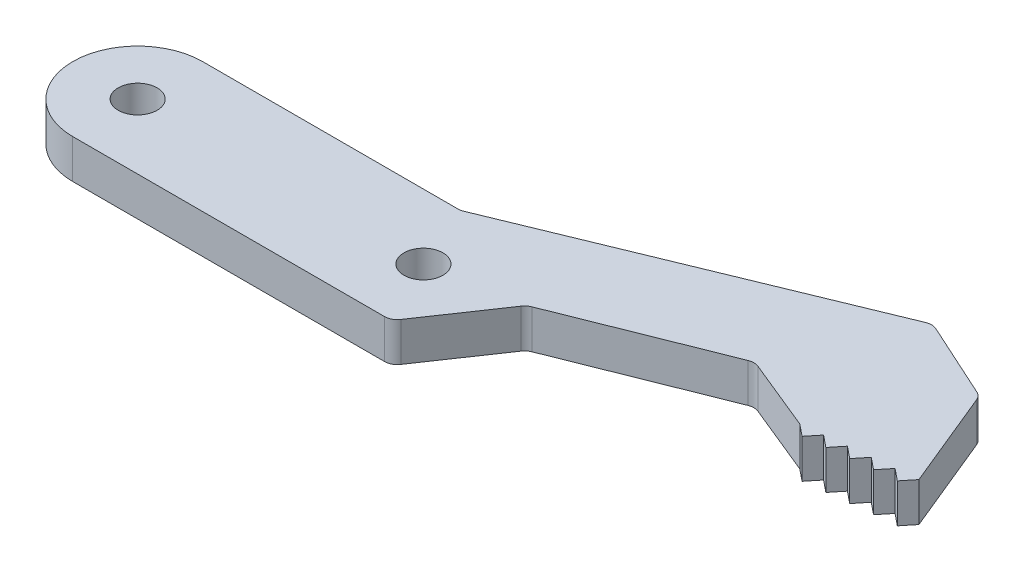
SolidWorks part; units mm, degrees
ref_plane "Front Plane" through (0, 0, 0) normal (0, 0, 1) x (1, 0, 0)
ref_plane "Top Plane" through (0, 0, 0) normal (0, 1, 0) x (1, 0, 0)
ref_plane "Right Plane" through (0, 0, 0) normal (1, 0, 0) x (0, 0, -1)
sketch "Sketch1" plane through (0, 0, 0) normal (0, 1, 0) x (1, 0, 0)
  line L1 (0, -5) -> (23.9989, -5)
  line L2 (0, 5) -> (19.6524, 5)
  line L3 (20.0327, 5.0751) -> (45.2294, 15.4347)
  line L4 (46.0242, 15.4199) -> (51.8314, 12.7746)
  line L5 (52.3417, 12.2448) -> (55.4426, 4.7029)
  line L6 (24.8266, -4.5611) -> (28.5649, 0.9541)
  line L7 (29.0223, 1.322) -> (40.9296, 6.07)
  line L8 (41.6788, 6.0666) -> (47.1446, 3.8294)
  line L11 (47.1446, 3.8294) -> (48.0617, 3.087)
  line L12 (48.0617, 3.087) -> (48.8042, 4.0041)
  line L13 (48.8042, 4.0041) -> (49.7213, 3.2617)
  line L14 (49.7213, 3.2617) -> (50.4638, 4.1788)
  line L15 (50.4638, 4.1788) -> (51.3809, 3.4364)
  line L16 (51.3809, 3.4364) -> (52.1234, 4.3535)
  line L17 (52.1234, 4.3535) -> (53.0405, 3.6111)
  line L18 (53.0405, 3.6111) -> (53.783, 4.5282)
  line L19 (53.783, 4.5282) -> (54.7001, 3.7858)
  line L20 (54.7001, 3.7858) -> (55.4426, 4.7029)
  circle A0 centre (0, 0) radius 1.5
  arc A1 (0, 5) -> (0, -5) centre (0, 0) ccw
  circle A2 centre (22, 0) radius 1.5
  arc A3 (28.5649, 0.9541) -> (29.0223, 1.322) centre (29.3927, 0.3931) cw
  arc A4 (40.9296, 6.07) -> (41.6788, 6.0666) centre (41.2999, 5.1412) cw
  arc A5 (51.8314, 12.7746) -> (52.3417, 12.2448) centre (51.4169, 11.8646) cw
  arc A6 (45.2294, 15.4347) -> (46.0242, 15.4199) centre (45.6096, 14.5098) cw
  arc A7 (19.6524, 5) -> (20.0327, 5.0751) centre (19.6524, 6) ccw
  arc A8 (23.9989, -5) -> (24.8266, -4.5611) centre (23.9989, -4) ccw
  point P18 (33.5141, 3.015)
  point P27 (28.7372, 1.2083)
  point P30 (41.3048, 6.2197)
  point P33 (52.1913, 12.6106)
  point P36 (45.63, 15.5994)
  point P39 (19.85, 5)
  point P42 (24.5291, -5)
  dimension "D1" = 3
  dimension "D2" = 10
  dimension "D4" = 3
  dimension "D20" = 1
  dimension "D3" = 22
  dimension "D5" = 124.13
  dimension "D6" = 7.5
  dimension "D7" = 214.13
  dimension "D8" = 13.53
  dimension "D9" = 224
  dimension "D10" = 6.31
  dimension "D11" = 157.65
  dimension "D12" = 19.85
  dimension "D13" = 25.78
  dimension "D14" = 7.21
  dimension "D15" = 133.16
  dimension "D16" = 136.84
  dimension "D17" = 8.55
  dimension "D18" = 1.18
  dimension "D19" = 1.18
extrude "Boss-Extrude1" add sketch "Sketch1" along normal blind 3
